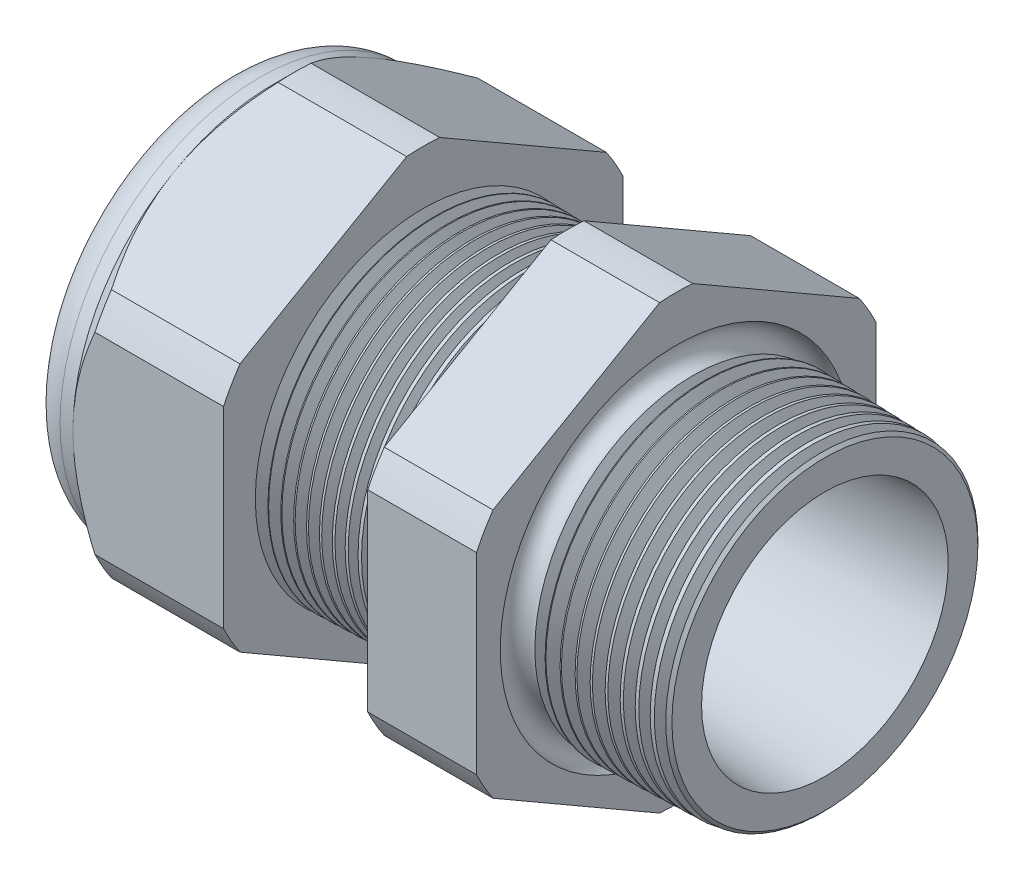
SolidWorks part; units mm, degrees
ref_plane "Front Plane" through (0, 0, 0) normal (0, 0, 1) x (1, 0, 0)
ref_plane "Top Plane" through (0, 0, 0) normal (0, 1, 0) x (1, 0, 0)
ref_plane "Right Plane" through (0, 0, 0) normal (1, 0, 0) x (0, 0, -1)
sketch "Sketch10" plane through (0, 0, 0) normal (0, 0, 1) x (1, 0, 0)
  line L0 (0, 0) -> (-115.3565, 0) construction
  line L1 (-34.798, 5.969) -> (-22.998, 5.969)
  line L2 (1.016, 7.3722) -> (1.016, 9.4042)
  line L3 (-7.874, 9.637) -> (1.016, 9.4042)
  line L4 (-7.874, 23.876) -> (-7.874, 9.637)
  line L5 (-7.874, 23.876) -> (-14.374, 23.876)
  line L6 (-14.374, 23.876) -> (-14.374, 9.8072)
  line L7 (-22.998, 10.033) -> (-14.374, 9.8072)
  line L8 (-22.998, 10.033) -> (-22.998, 23.876)
  line L9 (-22.998, 23.876) -> (-31.998, 23.876)
  line L10 (-31.998, 23.876) -> (-31.998, 11.938)
  line L11 (-31.998, 11.938) -> (-34.798, 11.938)
  line L12 (-34.798, 11.938) -> (-34.798, 5.969)
  line L13 (-22.998, 5.969) -> (1.016, 7.3722)
  dimension "D1" = 35.814
  dimension "D2" = 11.938
  dimension "D3" = 1.5
  dimension "D4" = 2.032
  dimension "A" = 20.066
  dimension "D6" = 23.876
  dimension "D8" = 47.752
  dimension "D9" = 2.8
  dimension "D10" = 9
  dimension "D11" = 6.5
  dimension "D" = 8.89
revolve "Revolve2" add sketch "Sketch10" angle 360 about L0
sketch "Sketch12" plane through (-31.998, 0, 0) normal (-1, 0, 0) x (0, 0, 1)
  line L1 (-0.9882, 13.2143) -> (-10.9498, 7.4629)
  line L2 (-11.938, 5.7513) -> (-11.938, -5.7513)
  line L3 (-10.9498, -7.4629) -> (-0.9882, -13.2143)
  line L4 (0.9882, -13.2143) -> (10.9498, -7.4629)
  line L5 (11.938, -5.7513) -> (11.938, 5.7513)
  line L6 (10.9498, 7.4629) -> (0.9882, 13.2143)
  circle A0 centre (0, 0) radius 11.938 construction
  arc A1 (0.9882, 13.2143) -> (-0.9882, 13.2143) centre (0, 0) ccw
  arc A2 (-10.9498, 7.4629) -> (-11.938, 5.7513) centre (0, 0) ccw
  arc A3 (-11.938, -5.7513) -> (-10.9498, -7.4629) centre (0, 0) ccw
  arc A4 (-0.9882, -13.2143) -> (0.9882, -13.2143) centre (0, 0) ccw
  arc A5 (10.9498, -7.4629) -> (11.938, -5.7513) centre (0, 0) ccw
  arc A6 (11.938, 5.7513) -> (10.9498, 7.4629) centre (0, 0) ccw
  dimension "D2" = 26.5024
  dimension "D1" = 23.876
extrude "Cut-Extrude2" cut sketch "Sketch12" against normal through all flip side to cut
fillet "Fillet4" radius 2.032 1 edges at (-34.798, 0, -11.938)
sketch "Sketch19" plane through (-31.998, 0, 0) normal (-1, 0, 0) x (0, 0, 1)
  line L0 (11.938, 0) -> (11.938, 5.7513) construction
  circle A0 centre (0, 0) radius 11.938
extrude "Cut-Extrude3" cut sketch "Sketch19" against normal blind 2 draft 45 flip side to cut
chamfer "Chamfer1" distance 0.254 angle 45 1 edges at (1.016, 0, -9.4042)
sketch "Sketch21" plane through (-34.798, 0, 0) normal (-1, 0, 0) x (0, 0, 1)
  circle A0 centre (0, 0) radius 5.969
  circle A2 centre (0, 0) radius 5.969 construction
extrude "plug" add sketch "Sketch21" against normal blind 6.35 separate body
sketch "Sketch22" plane through (-34.798, 0, 0) normal (-1, 0, 0) x (0, 0, 1)
  circle A0 centre (0, 0) radius 5.715
  circle A1 centre (0, 0) radius 5.969 construction
  dimension "D1" = 0.254
extrude "Cut-Extrude4" cut sketch "Sketch22" against normal blind 0.508
sketch "Sketch27" plane through (-34.29, 0, 0) normal (-1, 0, 0) x (0, 0, 1)
  line L0 (-4.3624, 0) -> (4.3624, 0) construction
  circle A0 centre (-3.8024, 0) radius 1.905
  circle A1 centre (0, 0) radius 5.715 construction
  dimension "D1" = 0.0076
  dimension "holedia" = 3.81
extrude "plugholes" cut sketch "Sketch27" against normal through all
pattern_circular "CirPattern1" count 2 over 360 about axis through (0, 0, 0) along (1, 0, 0) of "plugholes"
sketch "Sketch28" [suppressed] plane through (-29.464, 0, 0) normal (-1, 0, 0) x (0, 0, 1)
  circle A0 centre (0, 0) radius 0.762
  dimension "midholedia" = 3.81
extrude "midhole" [suppressed] cut sketch "Sketch28" against normal through all
sketch "Sketch29" plane through (0, 0, 0) normal (0, 0, 1) x (1, 0, 0)
  line L0 (-22.998, 10.033) -> (-22.265, 10.0138)
  line L1 (-14.374, 9.8072) -> (-22.998, 10.033) construction
  line L2 (-22.265, 10.0138) -> (-22.6481, 9.3886)
  line L3 (-22.6481, 9.3886) -> (-22.998, 10.033)
  dimension "D1" = 60
  dimension "D2" = 60
  dimension "D3" = 0.635
revolve "Cut-Revolve1" cut sketch "Sketch29" angle 360 about axis through (0, 0, 0) along (-1, 0, 0)
pattern_linear "LPattern1" count 11 spacing 0.762 along (1, 0, 0) of "Cut-Revolve1"
sketch "Sketch30" plane through (0, 0, 0) normal (0, 0, 1) x (1, 0, 0)
  line L0 (-7.874, 9.637) -> (-6.9944, 9.6139)
  line L1 (-7.874, 13.2143) -> (-7.874, 7.4629) construction
  line L2 (0.7621, 9.4108) -> (-7.874, 9.637) construction
  line L3 (-6.9944, 9.6139) -> (-7.4542, 8.8637)
  line L4 (-7.4542, 8.8637) -> (-7.874, 9.637)
  dimension "D1" = 60
  dimension "D2" = 60
  dimension "D3" = 0.762
revolve "Cut-Revolve2" cut sketch "Sketch30" angle 360 about axis through (0, 0, 0) along (-1, 0, 0)
pattern_linear "LPattern2" count 10 spacing 0.889 along (1, 0, 0) of "Cut-Revolve2"
sketch "Sketch31" [suppressed] plane through (-38.354, 0, 0) normal (-1, 0, 0) x (0, 0, 1)
  line L0 (-1.905, 1.905) -> (1.905, 1.905)
  line L1 (-1.905, -1.905) -> (1.905, -1.905)
  circle A0 centre (0, 0) radius 1.905 construction
  arc A1 (-1.905, 1.905) -> (-1.905, -1.905) centre (-1.905, 0) ccw
  arc A2 (1.905, 1.905) -> (1.905, -1.905) centre (1.905, 0) cw
extrude "Cut-Extrude5" [suppressed] cut sketch "Sketch31" against normal through all
sketch "Sketch32" plane through (0, 0, 0) normal (0, 0, 1) x (1, 0, 0)
  line L0 (-7.874, 13.2143) -> (-7.874, 7.4629) construction
  circle A0 centre (-7.747, 9.637) radius 0.889
  dimension "D2" = 1.778
  dimension "D1" = 0.127
revolve "Cut-Revolve3" cut sketch "Sketch32" angle 360 about axis through (0, 0, 0) along (-1, 0, 0)
